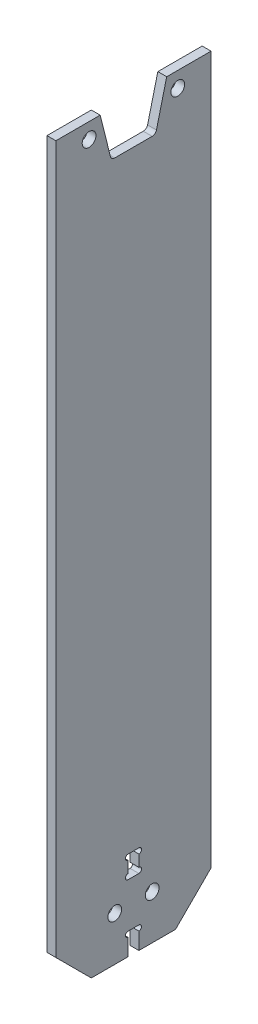
SolidWorks part; units mm, degrees
ref_plane "前视基准面" through (0, 0, 0) normal (0, 0, 1) x (1, 0, 0)
ref_plane "上视基准面" through (0, 0, 0) normal (0, 1, 0) x (1, 0, 0)
ref_plane "右视基准面" through (0, 0, 0) normal (1, 0, 0) x (0, 0, -1)
sketch "草图1" plane through (0, 0, 0) normal (1, 0, 0) x (0, 0, -1)
  line L5 (17.5, -83.75) -> (-17.5, -83.75)
  line L6 (17.5, -83.75) -> (17.5, 83.75)
  line L7 (17.5, 83.75) -> (-17.5, 83.75)
  line L8 (-17.5, -83.75) -> (-17.5, 83.75)
  line L9 (17.5, -83.75) -> (-17.5, 83.75) construction
  line L10 (17.5, 83.75) -> (-17.5, -83.75) construction
  point P0 (0, 0)
  dimension "D1" = 167.5
  dimension "D2" = 35
extrude "凸台-拉伸1" add sketch "草图1" along normal mid plane 2
sketch "草图2" plane through (1, 0, 0) normal (1, 0, 0) x (0, 0, -1)
  line L0 (-17.5, -83.75) -> (17.5, -83.75) construction
  line L1 (-1.225, -83.75) -> (1.225, -83.75)
  line L2 (-1.225, -83.75) -> (-1.225, -78.75)
  line L3 (-1.225, -78.75) -> (1.225, -78.75)
  line L4 (1.225, -83.75) -> (1.225, -78.75)
  point P6 (0, -78.75)
  dimension "D1" = 2.45
  dimension "D2" = 5
extrude "切除-拉伸1" cut sketch "草图2" against normal through all
sketch "草图3" plane through (1, 0, 0) normal (1, 0, 0) x (0, 0, -1)
  line L0 (-1.225, -78.75) -> (-1.225, -83.75) construction
  line L1 (1.225, -83.75) -> (1.225, -78.75) construction
  circle A0 centre (-1.225, -79.35) radius 0.6
  circle A1 centre (1.225, -79.35) radius 0.6
  dimension "D1" = 1.2
extrude "切除-拉伸2" cut sketch "草图3" against normal through all
sketch "草图5" plane through (1, 0, 0) normal (1, 0, 0) x (0, 0, -1)
  line L0 (-1.225, -63.7) -> (-1.225, -68.7)
  line L1 (-1.225, -68.7) -> (1.225, -68.7)
  line L2 (1.225, -68.7) -> (1.225, -63.7)
  line L3 (1.225, -63.7) -> (-1.225, -63.7)
  line L4 (-1.225, -79.95) -> (-1.225, -83.75) construction
  line L5 (1.225, -83.75) -> (1.225, -79.95) construction
  line L6 (1.225, -78.75) -> (-1.225, -78.75) construction
  dimension "D1" = 10.05
  dimension "D2" = 5
extrude "切除-拉伸4" cut sketch "草图5" against normal through all
sketch "草图6" plane through (1, 0, 0) normal (1, 0, 0) x (0, 0, -1)
  line L0 (-1.225, -63.7) -> (-1.225, -68.7) construction
  line L1 (1.225, -68.7) -> (1.225, -63.7) construction
  circle A0 centre (-1.225, -64.3) radius 0.6
  circle A1 centre (-1.225, -68.1) radius 0.6
  circle A2 centre (1.225, -64.3) radius 0.6
  circle A3 centre (1.225, -68.1) radius 0.6
  arc A4 (-1.225, -78.75) -> (-1.225, -79.95) centre (-1.225, -79.35) ccw construction
extrude "切除-拉伸5" cut sketch "草图6" against normal through all
sketch "草图7" plane through (1, 0, 0) normal (1, 0, 0) x (0, 0, -1)
  line L0 (0, -68.7) -> (0, -78.75) construction
  line L1 (-1.225, -68.7) -> (1.225, -68.7) construction
  line L2 (1.225, -78.75) -> (-1.225, -78.75) construction
  line L3 (-17.5, -83.75) -> (-1.225, -83.75) construction
  line L4 (-1.225, -64.9) -> (-1.225, -67.5) construction
  circle A0 centre (-4.225, -73.75) radius 1.55
  circle A1 centre (-4.225, -73.75) radius 3 construction
  circle A2 centre (4.225, -73.75) radius 1.55
  dimension "D1" = 10
  dimension "D2" = 3.1
  dimension "D3" = 6
extrude "切除-拉伸6" cut sketch "草图7" against normal through all
chamfer "倒角1" distance 8 angle 45 2 edges at (0, -83.75, -17.5) (0, -83.75, 17.5)
sketch "草图10" plane through (1, 0, 0) normal (1, 0, 0) x (0, 0, -1)
  line L0 (7.5, 83.75) -> (-7.5, 83.75)
  line L1 (17.5, 83.75) -> (-17.5, 83.75) construction
  line L2 (-7.5, 83.75) -> (-5, 73.75)
  line L3 (-5, 73.75) -> (5, 73.75)
  line L4 (5, 73.75) -> (7.5, 83.75)
  point P0 (0, 73.75)
  point P5 (0, 83.75)
  dimension "D1" = 15
  dimension "D2" = 10
  dimension "D3" = 10
extrude "切除-拉伸8" cut sketch "草图10" against normal through all
fillet "圆角1" radius 1 2 edges at (0, 73.75, 5) (0, 73.75, -5)
sketch "草图11" plane through (1, 0, 0) normal (1, 0, 0) x (0, 0, -1)
  line L0 (-10, 80.25) -> (10, 80.25) construction
  line L1 (-7.5, 83.75) -> (-17.5, 83.75) construction
  circle A0 centre (-10, 80.25) radius 1.55
  circle A1 centre (10, 80.25) radius 1.55
  point P4 (0, 80.25)
  dimension "D1" = 20
  dimension "D2" = 3.5
  dimension "D3" = 3.1
extrude "切除-拉伸9" cut sketch "草图11" against normal through all
